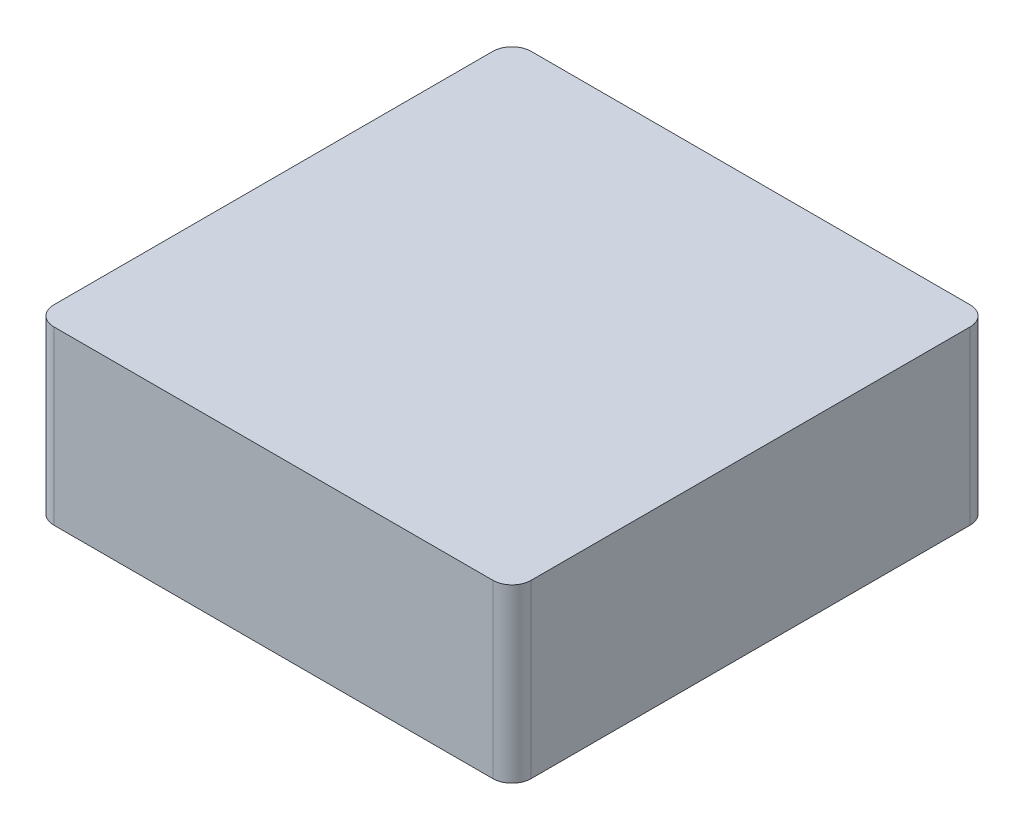
SolidWorks part; units mm, degrees
ref_plane "Front Plane" through (0, 0, 0) normal (0, 0, 1) x (1, 0, 0)
ref_plane "Top Plane" through (0, 0, 0) normal (0, 1, 0) x (1, 0, 0)
ref_plane "Right Plane" through (0, 0, 0) normal (1, 0, 0) x (0, 0, -1)
sketch "Sketch1" plane through (0, 0, 0) normal (0, 1, 0) x (1, 0, 0)
  line L1 (-12.5, -12.5) -> (12.5, -12.5)
  line L2 (-12.5, -12.5) -> (-12.5, 12.5)
  line L3 (-12.5, 12.5) -> (12.5, 12.5)
  line L4 (12.5, -12.5) -> (12.5, 12.5)
  line L5 (-12.5, -12.5) -> (12.5, 12.5) construction
  line L6 (-12.5, 12.5) -> (12.5, -12.5) construction
  point P4 (0, 0)
  point P5 (0, 0)
  dimension "D1" = 25
  dimension "D2" = 25
extrude "Boss-Extrude1" add sketch "Sketch1" along normal blind 9
fillet "Fillet1" radius 1 4 edges at (12.5, 4.5, -12.5) (12.5, 4.5, 12.5) (-12.5, 4.5, -12.5) (-12.5, 4.5, 12.5)
